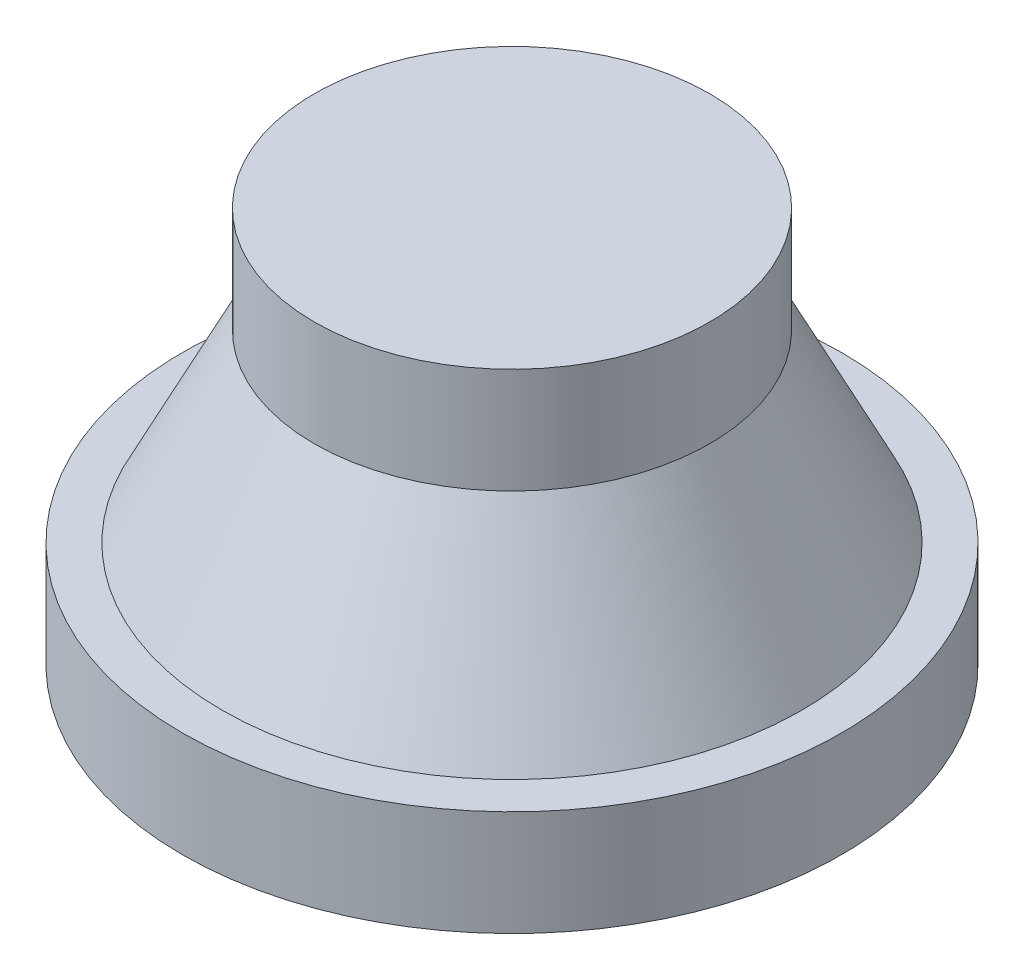
SolidWorks part; units mm, degrees
material "Cobre"
ref_plane "Plano frontal" through (0, 0, 0) normal (0, 0, 1) x (1, 0, 0)
ref_plane "Plano superior" through (0, 0, 0) normal (0, 1, 0) x (1, 0, 0)
ref_plane "Plano direito" through (0, 0, 0) normal (1, 0, 0) x (0, 0, -1)
sketch "Esboço1" plane through (0, 0, 0) normal (0, 1, 0) x (1, 0, 0)
  circle A0 centre (0, 0) radius 12.5
  dimension "D1" = 25
extrude "Ressalto-extrusão1" add sketch "Esboço1" along normal blind 15
sketch "Esboço2" plane through (0, 0, 0) normal (0, 0, 1) x (1, 0, 0)
  line L0 (0, 15) -> (0, 0) construction
  line L1 (12.5, 15) -> (-12.5, 15) construction
  line L2 (-12.5, 4) -> (-11, 4)
  line L3 (-12.5, 15) -> (-12.5, 0) construction
  line L4 (-11, 4) -> (-7.5, 11)
  line L5 (-7.5, 11) -> (-7.5, 15)
  line L6 (-7.5, 15) -> (-12.5, 15)
  line L7 (-12.5, 15) -> (-12.5, 4)
  line L8 (-12.5, 0) -> (12.5, 0) construction
  dimension "D1" = 5
  dimension "D2" = 1.5
  dimension "D3" = 4
  dimension "D4" = 4
revolve "Corte-Revolução1" cut sketch "Esboço2" angle 360 about L0
